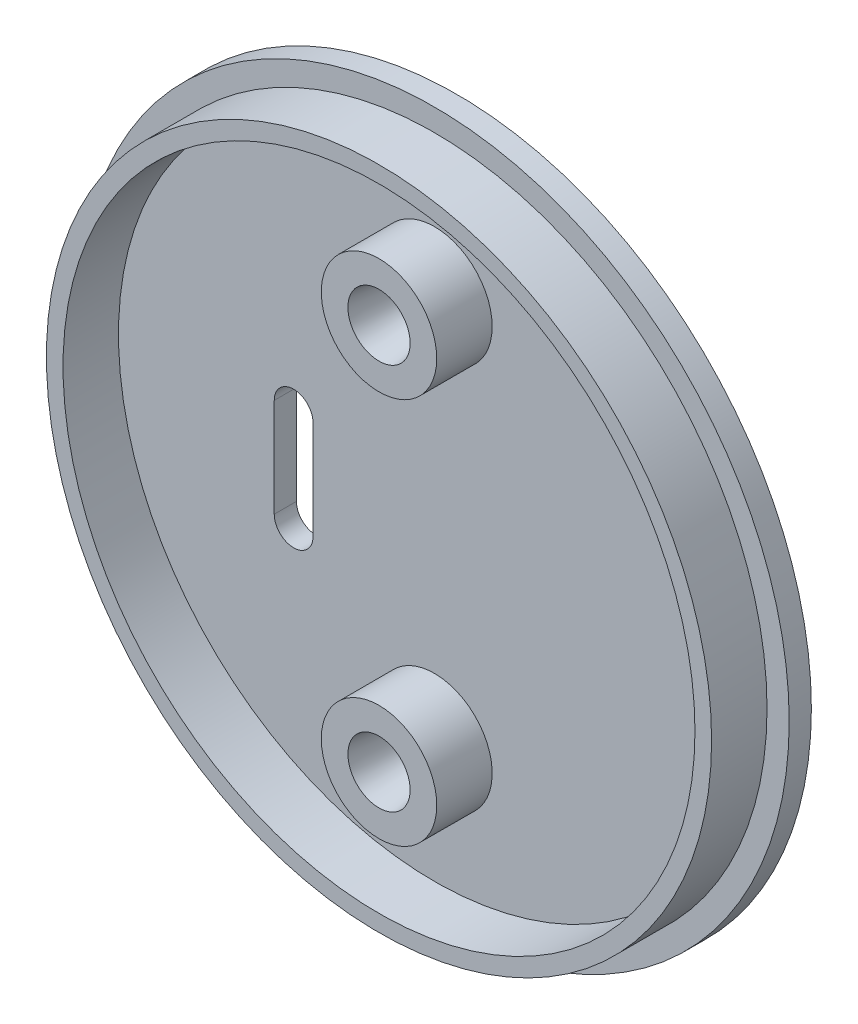
SolidWorks part; units mm, degrees
material "ABS"
ref_plane "X-Y Datum" through (0, 0, 0) normal (0, 0, 1) x (1, 0, 0)
ref_plane "X-Z Datum" through (0, 0, 0) normal (0, 1, 0) x (1, 0, 0)
ref_plane "Y-Z Datum" through (0, 0, 0) normal (1, 0, 0) x (0, 0, -1)
sketch "Sketch1" plane through (0, 0, 0) normal (0, 0, 1) x (1, 0, 0)
  circle A0 centre (0, 0) radius 32
  dimension "D1" = 64
extrude "Boss-Extrude1" add sketch "Sketch1" along normal mid plane 2
sketch "Sketch8" plane through (0, 0, 1) normal (0, 0, 1) x (1, 0, 0)
  circle A1 centre (0, 0) radius 28.5
  circle A2 centre (0, 0) radius 30
  circle A3 centre (0, 0) radius 30
  dimension "D1" = 2
  dimension "D2" = 1.5
extrude "Boss-Extrude4" add sketch "Sketch8" along normal blind 5
sketch "Sketch9" plane through (0, 0, 1) normal (0, 0, 1) x (1, 0, 0)
  line L0 (0, 17.4498) -> (0, -17.4498) construction
  line L1 (3.85, 0) -> (-3.85, 0) construction
  circle A0 centre (0, 17.4498) radius 5.207
  circle A1 centre (0, -17.4498) radius 5.207
  dimension "D2" = 10.414
  dimension "D1" = 34.8996
extrude "Boss-Extrude5" add sketch "Sketch9" along normal up to surface (5 mm away)
sketch "Sketch7" plane through (0, 0, -1) normal (0, 0, -1) x (-1, 0, 0)
  line L0 (12.7, 1.8542) -> (12.7, -7.0358) construction
  line L1 (14.45, 1.8542) -> (14.45, -7.0358)
  line L2 (10.95, 1.8542) -> (10.95, -7.0358)
  circle A0 centre (12.7, 0.8382) radius 0.9525 construction
  circle A1 centre (12.7, -2.5908) radius 0.9525 construction
  circle A2 centre (12.7, -6.1468) radius 0.9525 construction
  circle A3 centre (12.7, 0.8382) radius 0.9525 construction
  circle A4 centre (12.7, -2.5908) radius 0.9525 construction
  circle A5 centre (12.7, -6.1468) radius 0.9525 construction
  arc A6 (14.45, 1.8542) -> (10.95, 1.8542) centre (12.7, 1.8542) ccw
  arc A7 (10.95, -7.0358) -> (14.45, -7.0358) centre (12.7, -7.0358) ccw
  point P11 (12.7, -2.5908)
  dimension "D2" = 8.89
  dimension "D1" = 3.5
extrude "Cut-Extrude1" cut sketch "Sketch7" against normal through all and the other way through all
sketch "Sketch10" plane through (0, 0, 6) normal (0, 0, 1) x (1, 0, 0)
  circle A0 centre (0, 17.4498) radius 2.8067
  circle A1 centre (0, -17.4498) radius 2.8067
  dimension "D1" = 5.6134
extrude "Cut-Extrude2" cut sketch "Sketch10" against normal blind 4.7 draft 8
